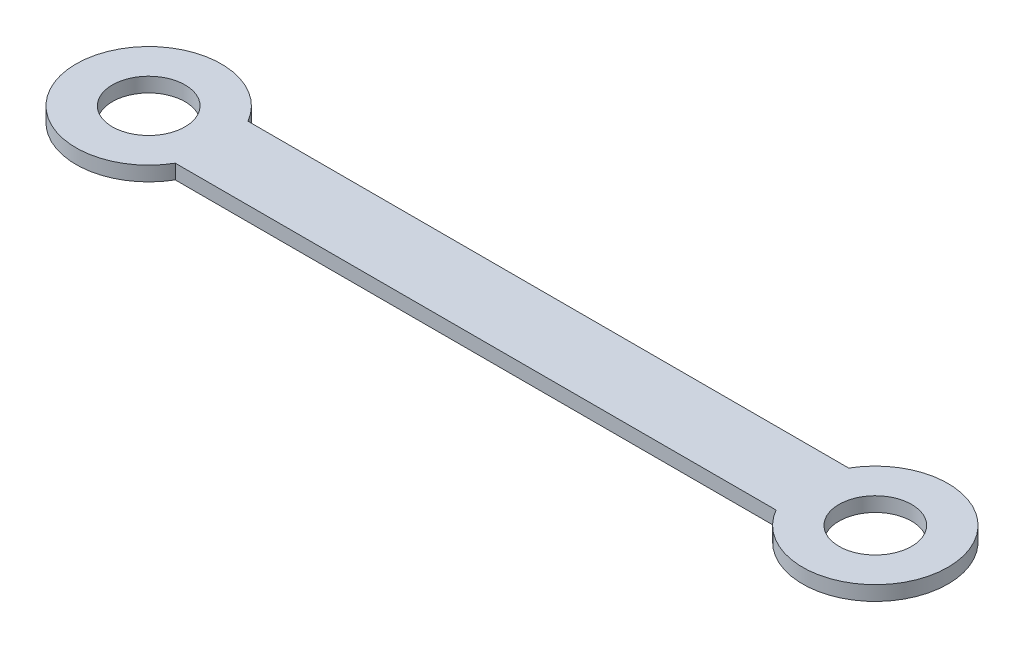
SolidWorks part; units mm, degrees
ref_plane "前基準面" through (0, 0, 0) normal (0, 0, 1) x (1, 0, 0)
ref_plane "上基準面" through (0, 0, 0) normal (0, 1, 0) x (1, 0, 0)
ref_plane "右基準面" through (0, 0, 0) normal (1, 0, 0) x (0, 0, -1)
sketch "草圖5" plane through (0, 0, 0) normal (0, 1, 0) x (1, 0, 0)
  line L0 (8.6603, -5) -> (91.3397, -5)
  line L2 (91.3397, 5) -> (8.6603, 5)
  circle A0 centre (0, 0) radius 5
  arc A1 (8.6603, 5) -> (8.6603, -5) centre (0, 0) ccw
  arc A2 (91.3397, -5) -> (91.3397, 5) centre (100, 0) ccw
  circle A3 centre (100, 0) radius 5
  dimension "D1" = 10
  dimension "D2" = 10
  dimension "D3" = 10
  dimension "D4" = 100
extrude "填料-伸長1" add sketch "草圖5" along normal blind 2
